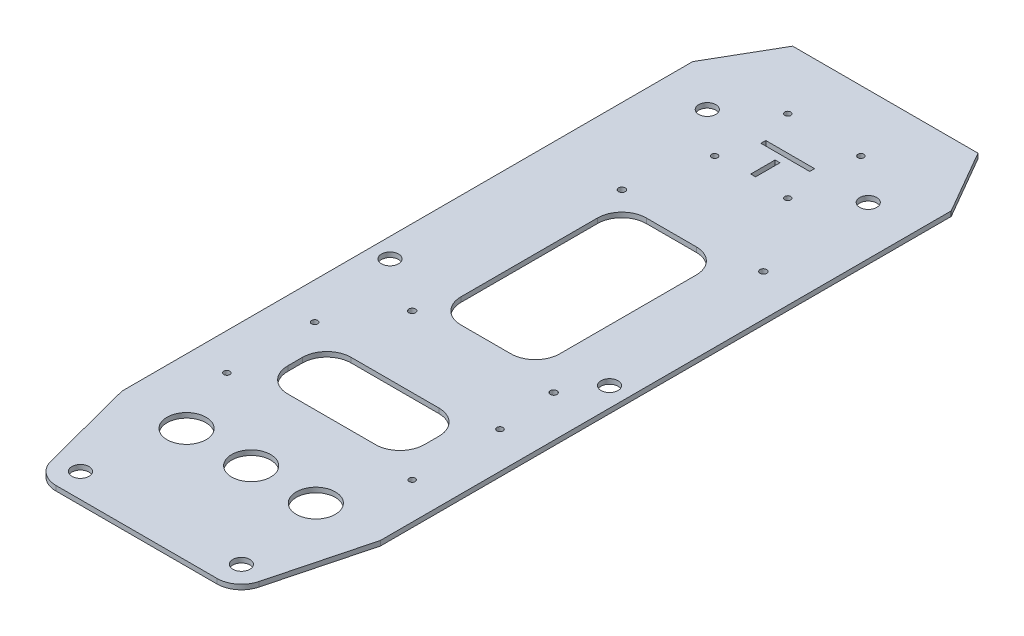
SolidWorks part; units mm, degrees
material "Epoxy, renforcé"
ref_plane "Plan de face" through (0, 0, 0) normal (0, 0, 1) x (1, 0, 0)
ref_plane "Plan de dessus" through (0, 0, 0) normal (0, 1, 0) x (1, 0, 0)
ref_plane "Plan de droite" through (0, 0, 0) normal (1, 0, 0) x (0, 0, -1)
sketch "Esquisse1" plane through (0, 0, 0) normal (0, 1, 0) x (1, 0, 0)
  line L0 (-33, 128.5) -> (33, 128.5) construction
  line L1 (33, 128.5) -> (33, -128.5) construction
  line L2 (33, -128.5) -> (-33, -128.5) construction
  line L3 (-33, -128.5) -> (-33, 128.5) construction
  line L4 (0, 128.5) -> (0, 0) construction
  line L5 (33, 0) -> (0, 0) construction
  line L6 (53, 168.5) -> (-53, 168.5)
  line L7 (-53, 168.5) -> (-53, -148.5)
  line L8 (-53, -148.5) -> (53, -148.5)
  line L9 (53, 168.5) -> (53, -148.5)
  circle A0 centre (-33, 128.5) radius 3.5
  circle A1 centre (-33, -128.5) radius 3.5
  circle A2 centre (33, 128.5) radius 3.5
  circle A3 centre (33, -128.5) radius 3.5
  point P17 (0, -148.5)
  point P18 (0, 168.5)
  dimension "D1" = 7
  dimension "D2" = 7
  dimension "D3" = 7
  dimension "D4" = 7
  dimension "D5" = 66
  dimension "D6" = 257
  dimension "D7" = 40
  dimension "D8" = 20
  dimension "D9" = 20
extrude "Boss.-Extru.1" add sketch "Esquisse1" along normal blind 2
sketch "Esquisse3" plane through (0, 2, 0) normal (0, 1, 0) x (1, 0, 0)
  line L0 (-22, -3.5) -> (-22, 82.5) construction
  line L1 (-22, 82.5) -> (36, 82.5) construction
  line L2 (36, 82.5) -> (36, -3.5) construction
  line L3 (36, -3.5) -> (-22, -3.5) construction
  line L4 (53, -148.5) -> (53, 168.5) construction
  line L5 (53, 168.5) -> (-53, 168.5) construction
  circle A4 centre (-22, -3.5) radius 1.375
  circle A5 centre (-22, 82.5) radius 1.375
  circle A6 centre (36, 82.5) radius 1.375
  circle A7 centre (36, -3.5) radius 1.375
  dimension "D1" = 86
  dimension "D2" = 58
  dimension "D3" = 17
  dimension "D4" = 86
extrude "Enlèv. mat.-Extru.1" cut sketch "Esquisse3" against normal through all
chamfer "Chanfrein1" distance 15 angle 60 2 edges at (-53, 1, -168.5) (53, 1, -168.5)
sketch "Esquisse4" plane through (0, 2, 0) normal (0, 1, 0) x (1, 0, 0)
  line L0 (0, -63.5) -> (0, -148.5) construction
  line L1 (38, -63.5) -> (-38, -63.5) construction
  line L2 (38, -63.5) -> (38, -27.5) construction
  line L3 (38, -27.5) -> (-38, -27.5) construction
  line L4 (-38, -63.5) -> (-38, -27.5) construction
  line L5 (-53, -148.5) -> (53, -148.5) construction
  line L6 (38, 168.5) -> (-38, 168.5) construction
  line L7 (-28, -58.5) -> (28, -58.5)
  line L8 (-28, -58.5) -> (-28, -32.5)
  line L9 (-28, -32.5) -> (28, -32.5)
  line L10 (28, -58.5) -> (28, -32.5)
  circle A0 centre (38, -63.5) radius 1.25
  circle A1 centre (38, -27.5) radius 1.25
  circle A2 centre (-38, -63.5) radius 1.25
  circle A3 centre (-38, -27.5) radius 1.25
  dimension "D3" = 2.5
  dimension "D4" = 2.5
  dimension "D5" = 2.5
  dimension "D6" = 2.5
  dimension "D1" = 76
  dimension "D2" = 36
  dimension "D7" = 196
  dimension "D8" = 10
  dimension "D9" = 10
  dimension "D10" = 10
  dimension "D11" = 10
extrude "Enlèv. mat.-Extru.2" cut sketch "Esquisse4" against normal blind 10
fillet "Congé1" radius 10 4 edges at (28, 1, 58.5) (28, 1, 32.5) (-28, 1, 32.5) (-28, 1, 58.5)
sketch "Esquisse5" plane through (0, 2, 0) normal (0, 1, 0) x (1, 0, 0)
  line L1 (-22, -3.5) -> (36, -3.5) construction
  line L2 (-22, -3.5) -> (-22, 82.5) construction
  line L3 (-22, 82.5) -> (36, 82.5) construction
  line L4 (36, -3.5) -> (36, 82.5) construction
  line L5 (-17, 1.5) -> (23.5, 1.5)
  line L6 (-17, 1.5) -> (-17, 77.5)
  line L7 (-17, 77.5) -> (23.5, 77.5)
  line L8 (23.5, 1.5) -> (23.5, 77.5)
  dimension "D1" = 10
  dimension "D2" = 10
  dimension "D3" = 25
  dimension "D4" = 10
extrude "Enlèv. mat.-Extru.3" cut sketch "Esquisse5" against normal blind 10
fillet "Congé2" radius 10 4 edges at (23.5, 1, -1.5) (23.5, 1, -77.5) (-17, 1, -77.5) (-17, 1, -1.5)
sketch "Esquisse6" plane through (0, 2, 0) normal (0, 1, 0) x (1, 0, 0)
  line L0 (0, 168.5) -> (0, 128.5) construction
  line L2 (38, 168.5) -> (-38, 168.5) construction
  line L3 (15, 113.5) -> (-15, 113.5) construction
  line L4 (15, 113.5) -> (15, 143.5) construction
  line L5 (15, 143.5) -> (-15, 143.5) construction
  line L6 (-15, 113.5) -> (-15, 143.5) construction
  line L7 (15, 113.5) -> (-15, 143.5) construction
  line L8 (15, 143.5) -> (-15, 113.5) construction
  line L9 (-10, 127.5) -> (10, 127.5)
  line L10 (-10, 127.5) -> (-10, 129.5)
  line L11 (-10, 129.5) -> (10, 129.5)
  line L12 (10, 127.5) -> (10, 129.5)
  line L13 (-10, 127.5) -> (10, 129.5) construction
  line L14 (-10, 129.5) -> (10, 127.5) construction
  line L15 (-1.1799, 114.5) -> (0.8201, 114.5)
  line L16 (-1.1799, 114.5) -> (-1.1799, 124.5)
  line L17 (-1.1799, 124.5) -> (0.8201, 124.5)
  line L18 (0.8201, 114.5) -> (0.8201, 124.5)
  line L19 (-1.1799, 114.5) -> (0.8201, 124.5) construction
  line L20 (-1.1799, 124.5) -> (0.8201, 114.5) construction
  circle A0 centre (-15, 113.5) radius 1.25
  circle A1 centre (15, 113.5) radius 1.25
  circle A2 centre (-15, 143.5) radius 1.25
  circle A3 centre (15, 143.5) radius 1.25
  point P16 (-0.1799, 119.5)
  dimension "D4" = 2.5
  dimension "D5" = 2.5
  dimension "D6" = 2.5
  dimension "D7" = 2.5
  dimension "D1" = 30
  dimension "D2" = 30
  dimension "D3" = 40
  dimension "D8" = 20
  dimension "D9" = 2
  dimension "D10" = 10
  dimension "D11" = 2
  dimension "D12" = 3
extrude "Enlèv. mat.-Extru.4" cut sketch "Esquisse6" against normal blind 10
sketch "Esquisse7" plane through (0, 2, 0) normal (0, 1, 0) x (1, 0, 0)
  line L0 (0, -91.5) -> (0, -148.5) construction
  line L1 (-53, -148.5) -> (53, -148.5) construction
  line L2 (0, -91.5) -> (-53, -91.5) construction
  line L3 (-53, 142.5192) -> (-53, -148.5) construction
  line L4 (38, 168.5) -> (-38, 168.5) construction
  circle A0 centre (0, -91.5) radius 8
  circle A1 centre (-26.5, -91.5) radius 8
  circle A2 centre (26.5, -91.5) radius 8
  dimension "D1" = 16
  dimension "D3" = 16
  dimension "D2" = 260
extrude "Enlèv. mat.-Extru.5" cut sketch "Esquisse7" against normal blind 10
sketch "Esquisse8" plane through (0, 2, 0) normal (0, 1, 0) x (1, 0, 0)
  line L0 (38, 168.5) -> (-38, 168.5)
  line L1 (38, 168.5) -> (-38, 168.5) construction
  line L2 (-38, 168.5) -> (-53, 142.5192)
  line L3 (-53, 142.5192) -> (-53, -91.5)
  line L4 (-53, 142.5192) -> (-53, -148.5) construction
  line L5 (-53, -91.5) -> (-42.6754, -131.0272)
  line L6 (-33, -138.5) -> (33, -138.5)
  line L7 (0, -148.5) -> (0, 168.5) construction
  line L8 (-53, -148.5) -> (53, -148.5) construction
  line L9 (53, -91.5) -> (42.6754, -131.0272)
  line L10 (53, 142.5192) -> (53, -91.5)
  line L11 (38, 168.5) -> (53, 142.5192)
  arc A0 (-42.6754, -131.0272) -> (-33, -138.5) centre (-33, -128.5) ccw
  arc A1 (42.6754, -131.0272) -> (33, -138.5) centre (33, -128.5) cw
  point P22 (0, -138.5)
  dimension "D1" = 20
  dimension "D2" = 260
extrude "Enlèv. mat.-Extru.6" cut sketch "Esquisse8" against normal blind 10 flip side to cut
sketch "Esquisse9" plane through (0, 2, 0) normal (0, 1, 0) x (1, 0, 0)
  line L0 (53, 10.4239) -> (-53, 10.4239) construction
  line L1 (53, -91.5) -> (53, 142.5192) construction
  line L2 (-53, 142.5192) -> (-53, -91.5) construction
  circle A0 centre (45, 10.4239) radius 3.5
  circle A1 centre (-45, 10.4239) radius 3.5
  dimension "D1" = 7
  dimension "D3" = 7
  dimension "D2" = 8
  dimension "D4" = 8
extrude "Enlèv. mat.-Extru.7" cut sketch "Esquisse9" against normal blind 10
